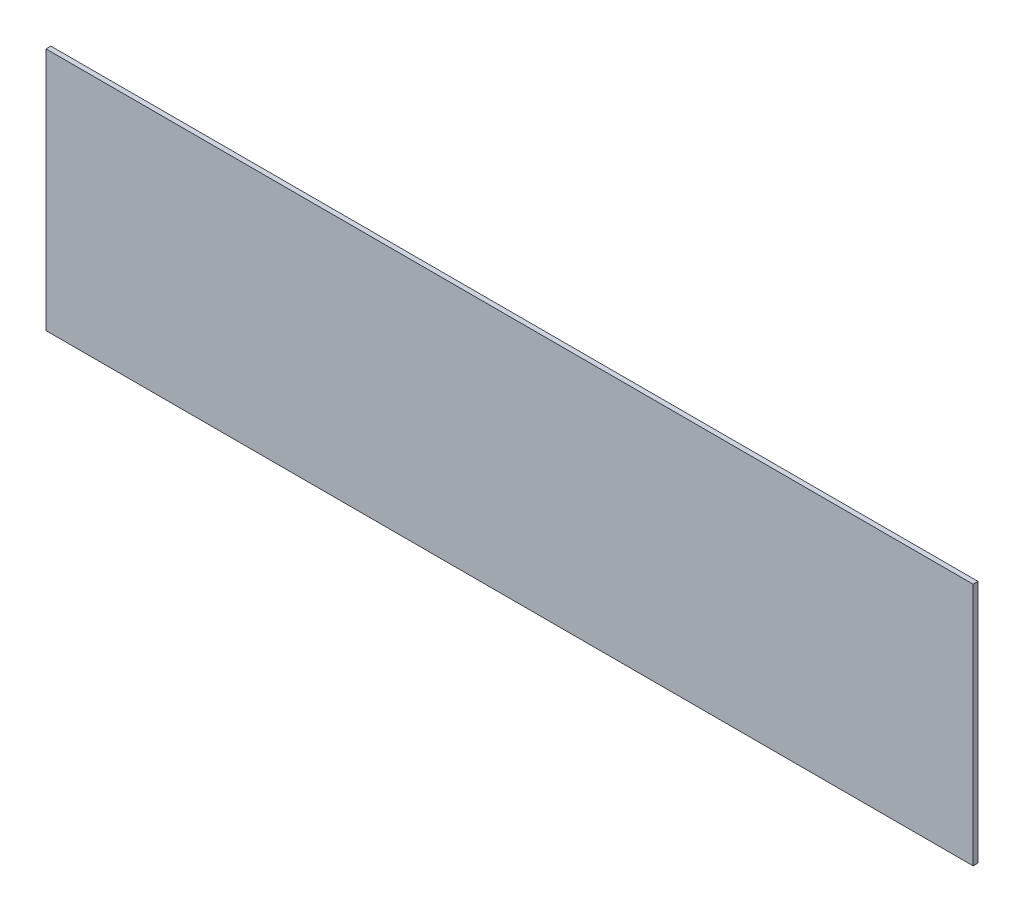
SolidWorks part; units mm, degrees
ref_plane "Front Plane" through (0, 0, 0) normal (0, 0, 1) x (1, 0, 0)
ref_plane "Top Plane" through (0, 0, 0) normal (0, 1, 0) x (1, 0, 0)
ref_plane "Right Plane" through (0, 0, 0) normal (1, 0, 0) x (0, 0, -1)
sketch "Sketch1" plane through (0, 0, 0) normal (0, 0, 1) x (1, 0, 0)
  line L1 (-285, 75) -> (285, 75)
  line L2 (-285, 75) -> (-285, -75)
  line L3 (-285, -75) -> (285, -75)
  line L4 (285, 75) -> (285, -75)
  line L5 (-285, 75) -> (285, -75) construction
  line L6 (-285, -75) -> (285, 75) construction
  point P0 (0, 0)
  dimension "D1" = 150
  dimension "D2" = 570
extrude "Boss-Extrude1" add sketch "Sketch1" along normal blind 3
